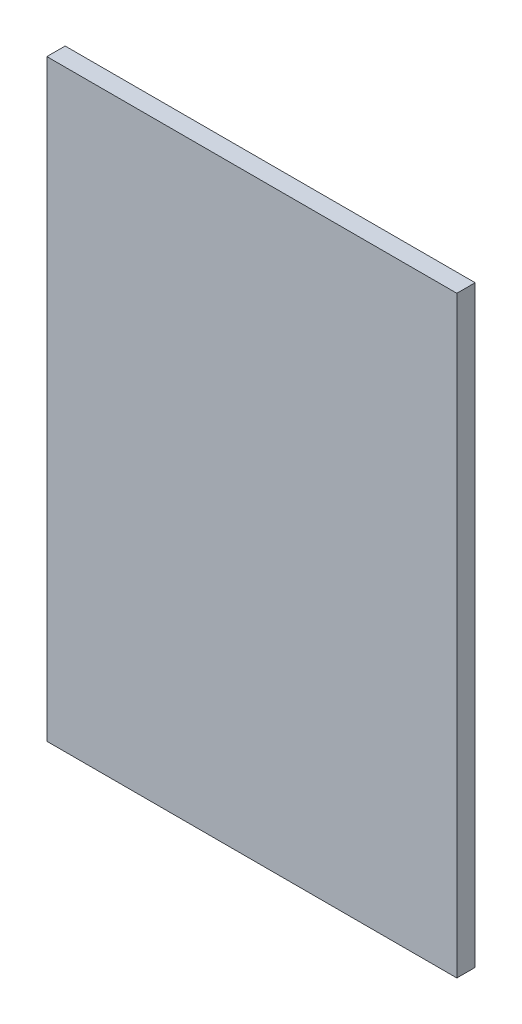
SolidWorks part; units mm, degrees
ref_plane "Front Plane" through (0, 0, 0) normal (0, 0, 1) x (1, 0, 0)
ref_plane "Top Plane" through (0, 0, 0) normal (0, 1, 0) x (1, 0, 0)
ref_plane "Right Plane" through (0, 0, 0) normal (1, 0, 0) x (0, 0, -1)
sketch "Sketch1" plane through (0, 0, 0) normal (0, 0, 1) x (1, 0, 0)
  line L0 (0, 0) -> (0, 82.296)
  line L1 (0, 82.296) -> (56.896, 82.296)
  line L2 (56.896, 82.296) -> (56.896, 0)
  line L3 (56.896, 0) -> (0, 0)
extrude "Boss-Extrude1" add sketch "Sketch1" along normal blind 2.54
